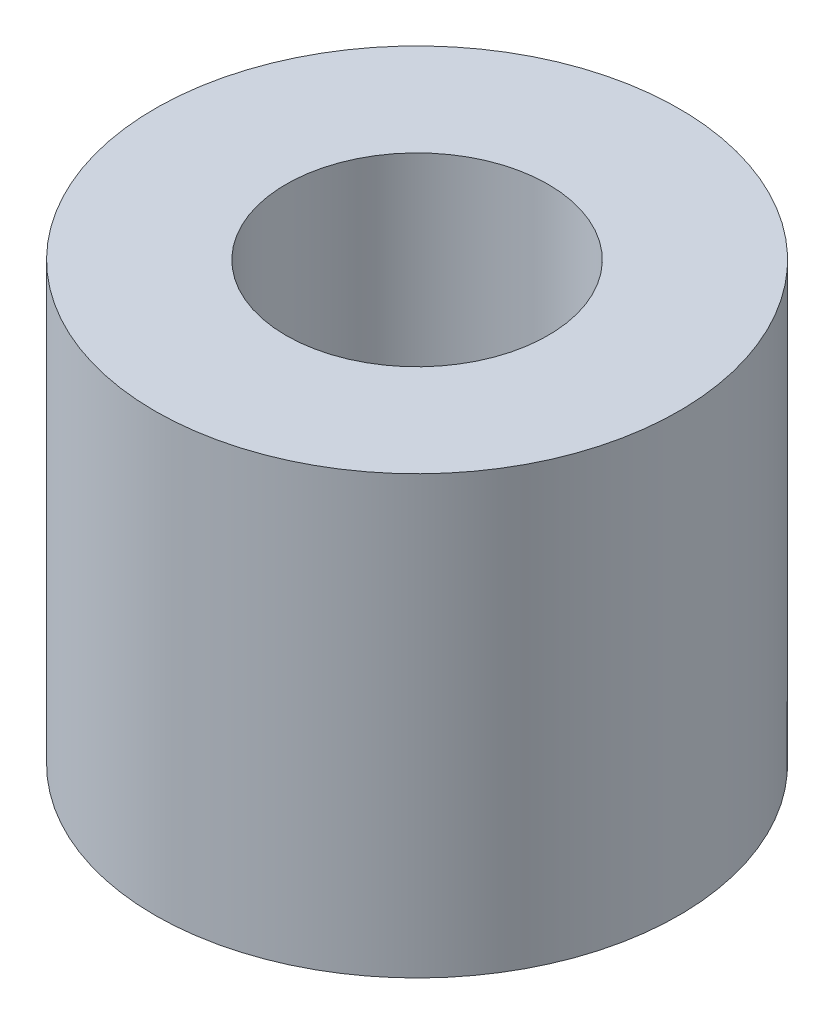
SolidWorks part; units mm, degrees
ref_plane "Front Plane" through (0, 0, 0) normal (0, 0, 1) x (1, 0, 0)
ref_plane "Top Plane" through (0, 0, 0) normal (0, 1, 0) x (1, 0, 0)
ref_plane "Right Plane" through (0, 0, 0) normal (1, 0, 0) x (0, 0, -1)
sketch "Sketch1" plane through (0, 0, 0) normal (0, 1, 0) x (1, 0, 0)
  circle A0 centre (0, 0) radius 1.5
  circle A1 centre (0, 0) radius 3
extrude "Boss-Extrude1" add sketch "Sketch1" along normal blind 5
